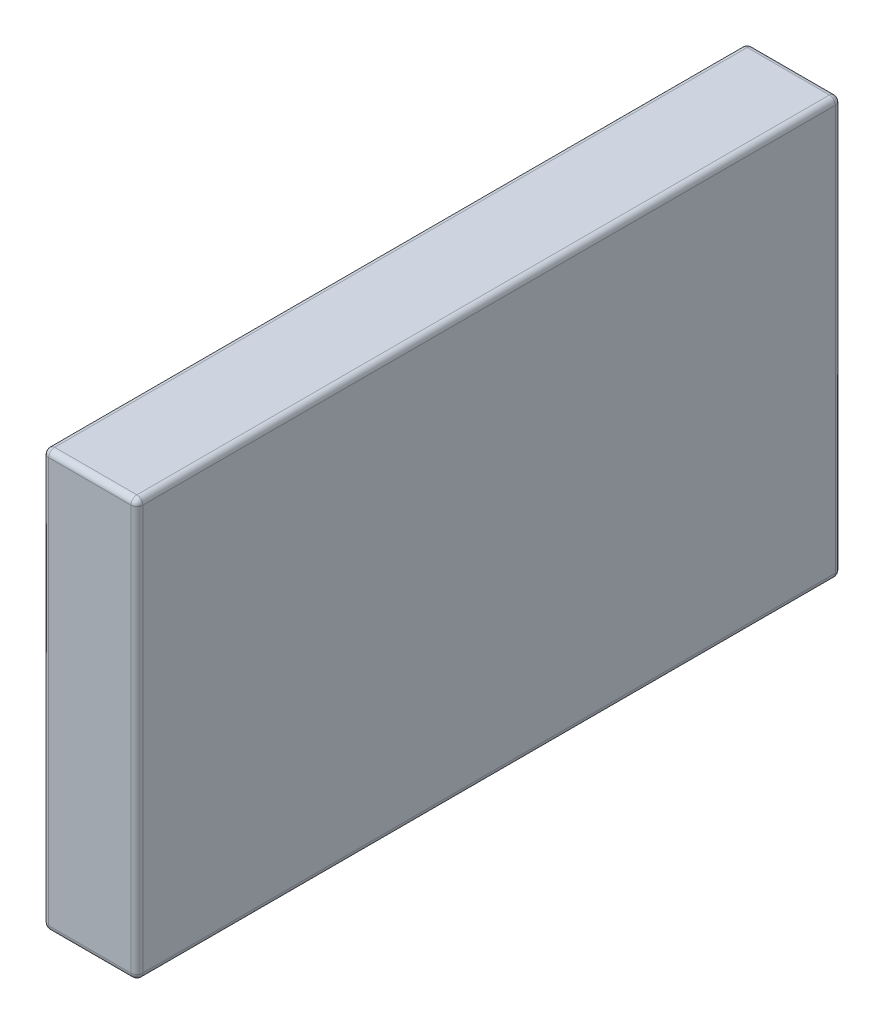
SolidWorks part; units mm, degrees
ref_plane "Front Plane" through (0, 0, 0) normal (0, 0, 1) x (1, 0, 0)
ref_plane "Top Plane" through (0, 0, 0) normal (0, 1, 0) x (1, 0, 0)
ref_plane "Right Plane" through (0, 0, 0) normal (1, 0, 0) x (0, 0, -1)
sketch "Sketch1" plane through (0, 0, 0) normal (0, 1, 0) x (1, 0, 0)
  line L1 (10.033, -75.057) -> (-10.033, -75.057)
  line L2 (10.033, -75.057) -> (10.033, 75.057)
  line L3 (10.033, 75.057) -> (-10.033, 75.057)
  line L4 (-10.033, -75.057) -> (-10.033, 75.057)
  line L5 (10.033, -75.057) -> (-10.033, 75.057) construction
  line L6 (10.033, 75.057) -> (-10.033, -75.057) construction
  point P0 (0, 0)
  dimension "D1" = 20.066
  dimension "D2" = 150.114
extrude "Boss-Extrude1" add sketch "Sketch1" along normal mid plane 88.9
fillet "Fillet1" radius 1.27 12 edges at (0, -44.45, -75.057) (-10.033, 0, -75.057) (-10.033, -44.45, 0) (-10.033, 0, 75.057) (0, -44.45, 75.057) (0, 44.45, -75.057) (0, 44.45, 75.057) (-10.033, 44.45, 0) (10.033, 0, 75.057) (10.033, 44.45, 0) (10.033, 0, -75.057) (10.033, -44.45, 0)
